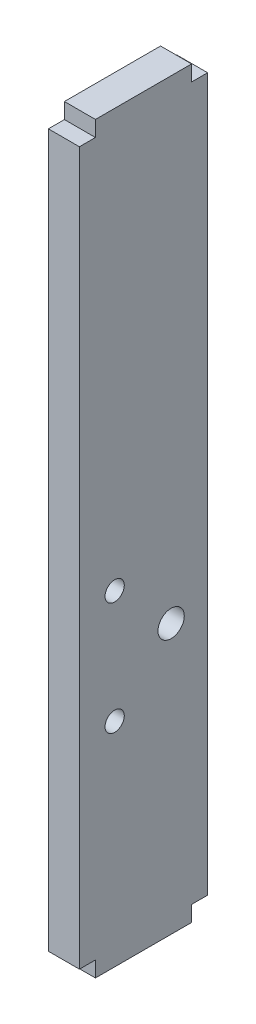
SolidWorks part; units mm, degrees
ref_plane "Alzado" through (0, 0, 0) normal (0, 0, 1) x (1, 0, 0)
ref_plane "Planta" through (0, 0, 0) normal (0, 1, 0) x (1, 0, 0)
ref_plane "Vista lateral" through (0, 0, 0) normal (1, 0, 0) x (0, 0, -1)
sketch "Croquis1" plane through (0, 0, 0) normal (1, 0, 0) x (0, 0, -1)
  line L0 (0, 0) -> (-10, 0) construction
  line L1 (-10, 0) -> (-10, 71.56)
  line L2 (-10, 71.56) -> (-7.5, 71.56)
  line L3 (-7.5, 71.56) -> (-7.5, 74)
  line L4 (-7.5, 74) -> (7.5, 74)
  line L5 (7.5, 74) -> (7.5, 71.56)
  line L6 (7.5, 71.56) -> (10, 71.56)
  line L7 (-10, 0) -> (-10, -39.56)
  line L8 (10, 71.56) -> (10, -39.56)
  line L9 (-10, -39.56) -> (-7.5, -39.56)
  line L10 (7.5, -39.56) -> (10, -39.56)
  line L11 (-7.5, -42) -> (7.5, -42)
  line L12 (-7.5, -42) -> (-7.5, -39.56)
  line L14 (7.5, -42) -> (7.5, -39.56)
  line L15 (-7.5, -42) -> (7.5, -39.56) construction
  line L16 (-7.5, -39.56) -> (7.5, -42) construction
  circle A0 centre (4.31, 0) radius 2.05
  circle A1 centre (-4.5, 8.81) radius 1.5
  circle A2 centre (-4.5, -8.81) radius 1.5
  point P11 (0, -40.78)
  dimension "D11" = 4.1
  dimension "D14" = 3
  dimension "D1" = 10
  dimension "D2" = 71.56
  dimension "D3" = 2.5
  dimension "D4" = 2.44
  dimension "D5" = 15
  dimension "D6" = 2.5
  dimension "D7" = 39.56
  dimension "D8" = 15
  dimension "D9" = 2.44
  dimension "D10" = 14.31
  dimension "D12" = 8.81
  dimension "D13" = 5.5
extrude "Saliente-Extruir1" add sketch "Croquis1" along normal blind 4.84
